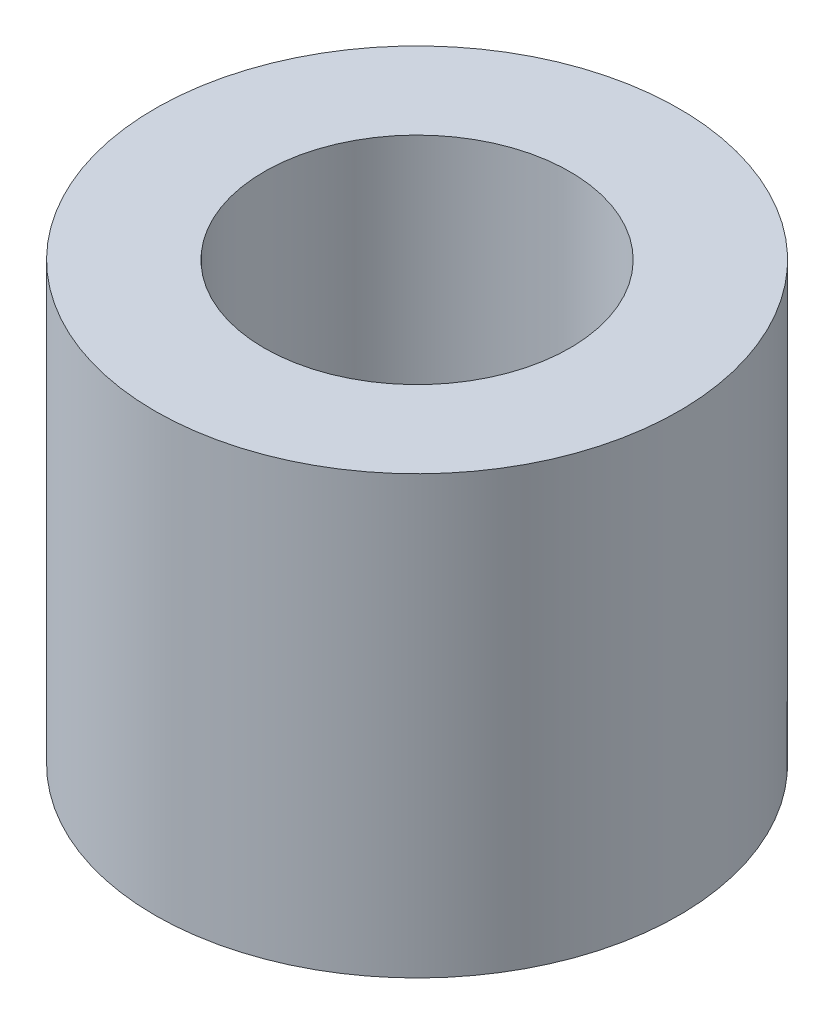
SolidWorks part; units mm, degrees
ref_plane "正面(Front)" through (0, 0, 0) normal (0, 0, 1) x (1, 0, 0)
ref_plane "平面(Top)" through (0, 0, 0) normal (0, 1, 0) x (1, 0, 0)
ref_plane "右側面(Right)" through (0, 0, 0) normal (1, 0, 0) x (0, 0, -1)
sketch "ｽｹｯﾁ1" plane through (0, 0, 0) normal (0, 1, 0) x (1, 0, 0)
  circle A0 centre (0, 0) radius 3
  circle A1 centre (0, 0) radius 1.75
  dimension "D1" = 6
  dimension "D2" = 3.5
extrude "ﾎﾞｽ - 押し出し1" add sketch "ｽｹｯﾁ1" along normal blind 5
